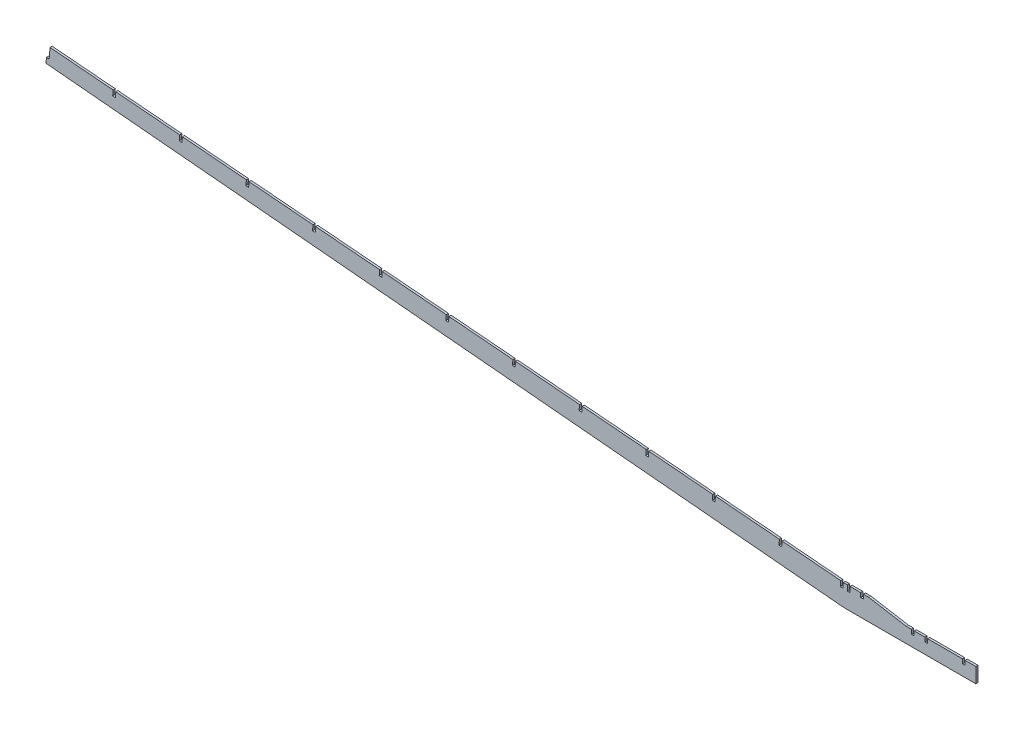
SolidWorks part; units mm, degrees
material "Plywood"
ref_plane "Front Plane" through (0, 0, 0) normal (0, 0, 1) x (1, 0, 0)
ref_plane "Top Plane" through (0, 0, 0) normal (0, 1, 0) x (1, 0, 0)
ref_plane "Right Plane" through (0, 0, 0) normal (1, 0, 0) x (0, 0, -1)
sketch "Sketch1" plane through (0, 0, 0) normal (0, 0, 1) x (1, 0, 0)
  line L0 (-949.6524, 80.0757) -> (-9.8872, -5.2596)
  line L1 (-945.9572, 86.1378) -> (-949.6524, 80.0757)
  line L8 (-6.7234, -5.5253) -> (-5.1293, 13.4579)
  line L9 (-5.1293, 13.4579) -> (-8.2932, 13.7235)
  line L10 (-8.2932, 13.7235) -> (-9.8872, -5.2596)
  line L11 (-9.8872, -5.2596) -> (-6.7234, -5.5253)
  line L12 (3.175, -5.8337) -> (3.175, 13.2163)
  line L13 (3.175, 13.2163) -> (0, 13.2163)
  line L14 (0, 13.2163) -> (0, -5.8337)
  line L15 (0, -5.8337) -> (3.175, -5.8337)
  line L17 (-943.1142, 119.9943) -> (-945.9572, 86.1378)
  line L18 (-945.9572, 86.1378) -> (-9.8872, -5.2596)
  line L19 (-6.7234, -5.5253) -> (0, -5.8337)
  line L20 (3.175, -5.8337) -> (152.4, -5.8337)
  line L21 (152.4, -5.8337) -> (152.4, 11.9463)
  line L22 (152.4, 11.9463) -> (69.85, 11.9463)
  line L23 (69.85, 11.9463) -> (25.4, 19.5663)
  line L24 (25.4, 19.5663) -> (-1.9861, 19.5663)
  line L25 (-1.9861, 19.5663) -> (-944.8986, 98.7448)
  line L26 (0, 13.2163) -> (0, 19.5663)
  line L27 (3.175, 13.2163) -> (3.175, 19.5663)
  line L28 (-5.1293, 13.4579) -> (-4.598, 19.7856)
  line L29 (-8.2932, 13.7235) -> (-7.7618, 20.0513)
  line L30 (-8.2932, 13.7235) -> (-945.4292, 92.426)
  line L31 (15.875, 19.5663) -> (15.875, 14.4863)
  line L32 (15.875, 14.4863) -> (19.05, 14.4863)
  line L33 (19.05, 14.4863) -> (19.05, 19.5663)
  line L34 (76.2, 6.8663) -> (76.2, 11.9463)
  line L35 (76.2, 6.8663) -> (79.375, 6.8663)
  line L36 (79.375, 6.8663) -> (79.375, 11.9463)
  line L37 (92.075, 11.9463) -> (92.075, 6.8663)
  line L38 (92.075, 6.8663) -> (95.25, 6.8663)
  line L39 (95.25, 6.8663) -> (95.25, 11.9463)
  line L40 (136.525, 11.9463) -> (136.525, 6.8663)
  line L41 (136.525, 6.8663) -> (139.7, 6.8663)
  line L42 (139.7, 6.8663) -> (139.7, 11.9463)
  line L44 (-949.6524, 80.0757) -> (-949.1211, 86.4035)
  line L45 (-949.1211, 86.4035) -> (-945.959, 86.1163)
  dimension "D1" = 25.4
  dimension "D2" = 6.35
extrude "Boss-Extrude1" add sketch "Sketch1" along normal blind 2.54
sketch "Sketch2" plane through (0, 0, 2.54) normal (0, 0, 1) x (1, 0, 0)
  line L1 (-76.483, 72.8473) -> (-82.5095, 1.0799)
  line L3 (-155.6446, 77.1971) -> (-161.4339, 8.255)
  line L5 (-234.8005, 81.6162) -> (-240.3617, 15.3891)
  line L7 (-313.9625, 85.9617) -> (-319.2865, 22.5591)
  line L9 (-393.1191, 90.3714) -> (-398.2146, 29.6908)
  line L11 (-472.2837, 94.686) -> (-477.1388, 36.8682)
  line L13 (-551.4418, 99.0783) -> (-556.0668, 44.0001)
  line L15 (-630.6082, 103.3716) -> (-634.991, 51.1773)
  line L17 (-709.7674, 107.7507) -> (-713.9195, 58.3043)
  line L19 (-788.9364, 112.0121) -> (-792.8436, 65.483)
  line L21 (-868.0976, 116.3681) -> (-871.7723, 72.6069)
  line L23 (-73.3191, 72.5816) -> (-79.3456, 0.8143)
  line L25 (-152.4808, 76.9314) -> (-158.27, 7.9893)
  line L27 (-231.6366, 81.3506) -> (-237.1978, 15.1234)
  line L29 (-310.7986, 85.696) -> (-316.1227, 22.2934)
  line L31 (-389.9552, 90.1057) -> (-395.0507, 29.4251)
  line L33 (-469.1198, 94.4203) -> (-473.9749, 36.6025)
  line L35 (-548.2779, 98.8126) -> (-552.903, 43.7344)
  line L37 (-627.4443, 103.1059) -> (-631.8272, 50.9116)
  line L39 (-706.6035, 107.485) -> (-710.7556, 58.0386)
  line L41 (-785.7726, 111.7464) -> (-789.6797, 65.2173)
  line L43 (-864.9337, 116.1024) -> (-868.6084, 72.3413)
  line L45 (-8.2932, 13.7235) -> (-945.4292, 92.426)
  line L47 (-7.7618, 20.0513) -> (-944.8986, 98.7448)
extrude "Cut-Extrude1" cut sketch "Sketch2" against normal through all and the other way through all
move or copy body "Body-Move/Copy1" [suppressed] bodies to move or copy 102 parameters "D1"=0, "D2"=0, "D3"=0
